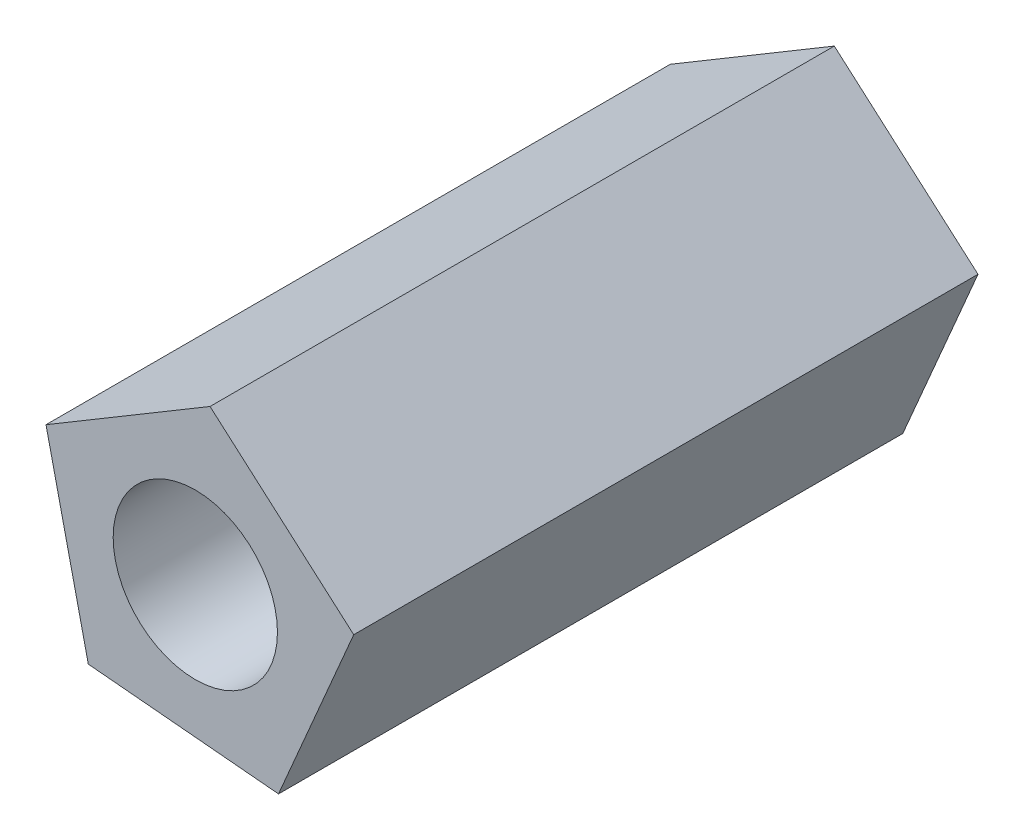
SolidWorks part; units mm, degrees
material "Alüminyum Bronz"
ref_plane "Ön Düzlem" through (0, 0, 0) normal (0, 0, 1) x (1, 0, 0)
ref_plane "Üst Düzlem" through (0, 0, 0) normal (0, 1, 0) x (1, 0, 0)
ref_plane "Sağ Düzlem" through (0, 0, 0) normal (1, 0, 0) x (0, 0, -1)
sketch "Çizim1" plane through (0, 0, 0) normal (0, 0, 1) x (1, 0, 0)
  line L1 (0.448, 4.9239) -> (-4.5445, 1.9476)
  line L2 (-4.5445, 1.9476) -> (-3.2566, -3.7202)
  line L3 (-3.2566, -3.7202) -> (2.5318, -4.2469)
  line L4 (2.5318, -4.2469) -> (4.8214, 1.0955)
  line L5 (4.8214, 1.0955) -> (0.448, 4.9239)
  circle A0 centre (0, 0) radius 2.5
  circle A1 centre (0, 0) radius 4 construction
extrude "Yükseklik-Ekstrüzyon1" add sketch "Çizim1" along normal blind 19
scale "Scale1" scale about centroid uniform scaling yes scale factor 0.5
